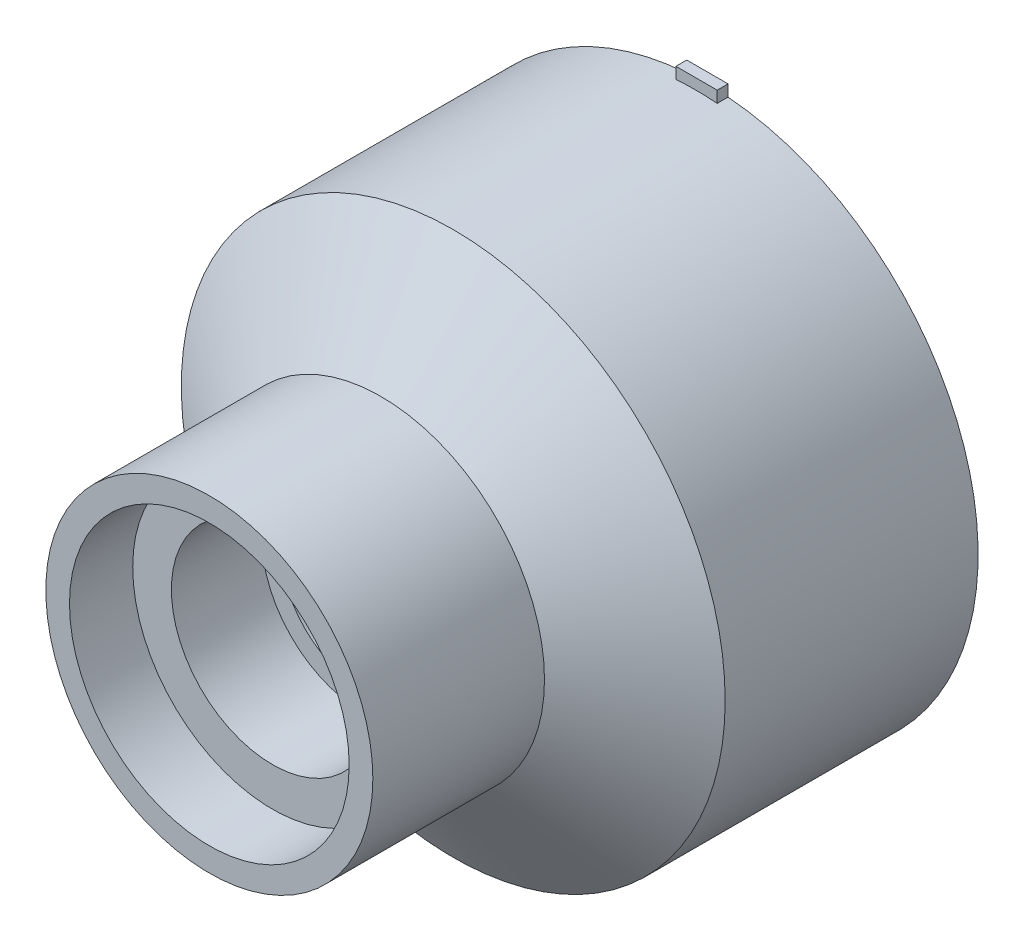
SolidWorks part; units mm, degrees
ref_plane "Alzado" through (0, 0, 0) normal (0, 0, 1) x (1, 0, 0)
ref_plane "Planta" through (0, 0, 0) normal (0, 1, 0) x (1, 0, 0)
ref_plane "Vista lateral" through (0, 0, 0) normal (1, 0, 0) x (0, 0, -1)
sketch "Croquis1" plane through (0, 0, 0) normal (0, 0, 1) x (1, 0, 0)
  circle A0 centre (0, 0) radius 15.05
  circle A1 centre (0, 0) radius 14.05
  dimension "D1" = 28.1
  dimension "D2" = 1
extrude "Saliente-Extruir1" add sketch "Croquis1" along normal blind 0.6
sketch "Croquis2" plane through (0, 0, 0) normal (0, 0, -1) x (-1, 0, 0)
  line L0 (-2.4048, 14.8566) -> (-2.4048, 13.8427)
  line L1 (2.4048, 14.8566) -> (2.4048, 13.8427)
  line L2 (0, 0) -> (0, 9.588) construction
  line L3 (0, 0) -> (9.588, 0) construction
  line L4 (14.8566, 2.4048) -> (13.8427, 2.4048)
  line L5 (14.8566, -2.4048) -> (13.8427, -2.4048)
  line L6 (0, 0) -> (0, -9.588) construction
  line L7 (2.4048, -14.8566) -> (2.4048, -13.8427)
  line L8 (-2.4048, -14.8566) -> (-2.4048, -13.8427)
  line L9 (0, 0) -> (-9.588, 0) construction
  line L10 (-14.8566, -2.4048) -> (-13.8427, -2.4048)
  line L11 (-14.8566, 2.4048) -> (-13.8427, 2.4048)
  circle A0 centre (0, 0) radius 14.05 construction
  circle A1 centre (0, 0) radius 15.05
  arc A2 (2.4048, 14.8566) -> (-2.4048, 14.8566) centre (0, 0) ccw
  arc A3 (2.4048, 13.8427) -> (-2.4048, 13.8427) centre (0, 0) ccw
  arc A4 (14.8566, -2.4048) -> (14.8566, 2.4048) centre (0, 0) ccw
  arc A5 (13.8427, -2.4048) -> (13.8427, 2.4048) centre (0, 0) ccw
  arc A6 (-2.4048, -14.8566) -> (2.4048, -14.8566) centre (0, 0) ccw
  arc A7 (-2.4048, -13.8427) -> (2.4048, -13.8427) centre (0, 0) ccw
  arc A8 (-14.8566, 2.4048) -> (-14.8566, -2.4048) centre (0, 0) ccw
  arc A9 (-13.8427, 2.4048) -> (-13.8427, -2.4048) centre (0, 0) ccw
  point P26 (0, 0)
  dimension "D1" = 0
  dimension "D2" = 4
extrude "Saliente-Extruir2" add sketch "Croquis2" along normal blind 0.4
sketch "Croquis3" plane through (0, 0, 0.6) normal (0, 0, 1) x (1, 0, 0)
  circle A0 centre (0, 0) radius 14.05 construction
  circle A1 centre (0, 0) radius 15.05
  circle A2 centre (0, 0) radius 15.05
  circle A3 centre (0, 0) radius 14.05
  dimension "D1" = 0
sketch "Croquis4" plane through (0, 0, 0) normal (1, 0, 0) x (0, 0, -1)
  line L0 (-0.6, 15.05) -> (-4.6, 9.05)
  line L1 (-0.6, 14.05) -> (-4.6, 8.05)
  line L2 (-4.6, 8.05) -> (-4.6, 9.05)
  line L3 (-0.6, 14.05) -> (-0.6, 9.8338) construction
  line L4 (-0.6, 9.8338) -> (-7.5387, 9.8338) construction
  line L5 (-0.6, 14.05) -> (-0.6, 15.05)
  line L6 (0, 0) -> (-10.1471, 0) construction
  line L7 (-4.6, 8.05) -> (3.2414, 8.05) construction
  line L8 (0.9449, 6.8844) -> (-4.6, 6.8844) construction
  dimension "D2" = 6
revolve "Revolución1" add sketch "Croquis4" angle 360 about L6
sketch "Croquis5" plane through (0, 0, 0) normal (0, 0, -1) x (-1, 0, 0)
  circle A0 centre (0, 0) radius 15.05 construction
  circle A1 centre (0, 0) radius 15.05
  circle A2 centre (0, 0) radius 14.05 construction
  circle A3 centre (0, 0) radius 14.05
extrude "Saliente-Extruir3" add sketch "Croquis5" along normal blind 0.4
sketch "Croquis6" plane through (0, 0, 4.6) normal (0, 0, 1) x (1, 0, 0)
  line L0 (0, 0) -> (0, 8.9051) construction
  line L1 (0, 0) -> (10.1298, 0) construction
  line L2 (-2.4961, 15.6365) -> (2.4961, 15.6365) construction
  line L3 (2.4961, 15.6365) -> (2.4961, 2.574)
  line L4 (-2.4961, 15.6365) -> (-2.4961, 2.574)
  line L5 (15.6383, -2.4979) -> (2.5514, -2.4094)
  line L6 (15.6383, 2.4943) -> (15.6383, -2.4979) construction
  line L7 (15.6383, 2.4943) -> (2.4961, 2.574)
  line L8 (-2.4961, -15.6401) -> (-2.545, -2.5217)
  line L9 (2.4961, -15.6401) -> (-2.4961, -15.6401) construction
  line L10 (2.4961, -15.6401) -> (2.5514, -2.4094)
  line L11 (-15.6383, 2.4943) -> (-2.4961, 2.574)
  line L12 (-15.6383, -2.4979) -> (-15.6383, 2.4943) construction
  line L13 (-15.6383, -2.4979) -> (-2.545, -2.5217)
  arc A0 (-15.6383, 2.4943) -> (-2.4961, 15.6365) centre (-2.4961, 2.4943) cw
  arc A1 (2.4961, 15.6365) -> (15.6383, 2.4943) centre (2.4961, 2.4943) cw
  arc A2 (15.6383, -2.4979) -> (2.4961, -15.6401) centre (2.4961, -2.4979) cw
  arc A3 (-2.4961, -15.6401) -> (-15.6383, -2.4979) centre (-2.4961, -2.4979) cw
  point P6 (0, 15.6365)
  point P24 (0, 0)
  point P34 (0, -0.0018)
  dimension "D1" = 4
sketch "Croquis7" plane through (0, 0, -0.4) normal (0, 0, -1) x (-1, 0, 0)
  circle A0 centre (0, 0) radius 14.05 construction
  circle A1 centre (0, 0) radius 15.05
  circle A2 centre (0, 0) radius 15.05
  circle A3 centre (0, 0) radius 14.05
  dimension "D1" = 0
extrude "Saliente-Extruir4" add sketch "Croquis7" along normal blind 13
sketch "Croquis8" plane through (0, 0, -13.4) normal (0, 0, -1) x (-1, 0, 0)
  line L0 (2.4961, 15.6365) -> (-2.4961, 15.6365) construction
  line L1 (-1.2079, 14.5143) -> (1.0785, 14.5143)
  line L2 (-1.2079, 14.5143) -> (-1.2079, 15.6365)
  line L3 (-1.2079, 15.6365) -> (1.0785, 15.6365)
  line L4 (1.0785, 14.5143) -> (1.0785, 15.6365)
extrude "Saliente-Extruir5" add sketch "Croquis8" against normal blind 0.6
sketch "Croquis10" plane through (0, 0, 4.6) normal (0, 0, 1) x (1, 0, 0)
  circle A0 centre (0, 0) radius 4.525
  circle A1 centre (0, 0) radius 6.525
  dimension "D1" = 9.05
  dimension "D2" = 2
extrude "Saliente-Extruir6" add sketch "Croquis10" along normal blind 1 separate body
sketch "Croquis11" plane through (0, 0, 5.6) normal (0, 0, 1) x (1, 0, 0)
  circle A0 centre (0, 0) radius 5.6
  circle A2 centre (0, 0) radius 9.05 construction
  circle A3 centre (0, 0) radius 9.05
  dimension "D1" = 11.2
extrude "Saliente-Extruir7" add sketch "Croquis11" along normal blind 5
sketch "Croquis12" plane through (0, 0, 4.6) normal (0, 0, 1) x (1, 0, 0)
  circle A0 centre (0, 0) radius 9.05 construction
  circle A1 centre (0, 0) radius 9.05
  circle A2 centre (0, 0) radius 8.05 construction
  circle A3 centre (0, 0) radius 8.05
extrude "Saliente-Extruir9" add sketch "Croquis12" along normal up to surface (1 mm away) up to face at (9.05, 0, 5.6)
sketch "Croquis13" plane through (0, 0, 10.6) normal (0, 0, 1) x (1, 0, 0)
  circle A0 centre (0, 0) radius 7.74
  circle A1 centre (0, 0) radius 9.05 construction
  circle A2 centre (0, 0) radius 9.05
  dimension "D1" = 15.48
extrude "Saliente-Extruir10" add sketch "Croquis13" along normal blind 3.5
sketch "Croquis14" plane through (0, 0, 4.6) normal (0, 0, -1) x (-1, 0, 0)
  circle A0 centre (0, 0) radius 6.525 construction
  circle A1 centre (0, 0) radius 6.525
  circle A2 centre (0, 0) radius 8.05 construction
  circle A3 centre (0, 0) radius 8.05
extrude "Saliente-Extruir11" add sketch "Croquis14" against normal up to surface (1 mm away) up to face at (8.05, 0, 5.6)
sketch "Croquis17" plane through (0, 0, -13.4) normal (0, 0, -1) x (-1, 0, 0)
  circle A0 centre (0, 0) radius 29.4895
